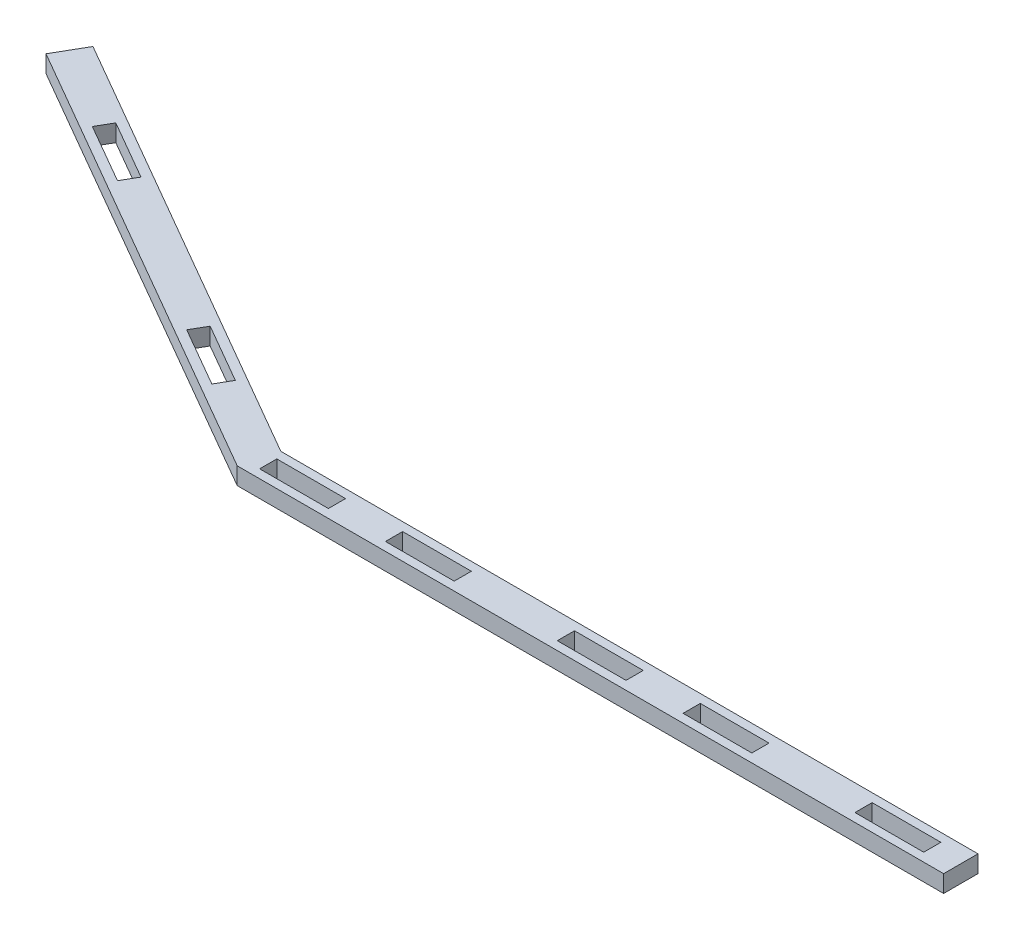
SolidWorks part; units mm, degrees
material "Cedar"
ref_plane "Front Plane" through (0, 0, 0) normal (0, 0, 1) x (1, 0, 0)
ref_plane "Top Plane" through (0, 0, 0) normal (0, 1, 0) x (1, 0, 0)
ref_plane "Right Plane" through (0, 0, 0) normal (1, 0, 0) x (0, 0, -1)
sketch "Sketch4" plane through (0, 0, 0) normal (0, 1, 0) x (1, 0, 0)
  line L0 (-428.2056, 90.1761) -> (-421.8556, 101.1746)
  line L1 (-421.8556, 101.1746) -> (-257.6145, 6.35)
  line L2 (-428.2056, 90.1761) -> (-261.0175, -6.35)
  line L3 (0, -6.35) -> (0, 6.35)
  line L4 (0, 6.35) -> (-257.6145, 6.35)
  line L5 (0, -6.35) -> (-261.0175, -6.35)
  line L6 (-396.3722, 75.4632) -> (-374.3751, 62.7632)
  line L7 (-374.3751, 62.7632) -> (-371.2001, 68.2625)
  line L8 (-371.2001, 68.2625) -> (-393.1972, 80.9625)
  line L9 (-393.1972, 80.9625) -> (-396.3722, 75.4632)
  line L10 (-313.8833, 27.8382) -> (-291.8862, 15.1382)
  line L11 (-291.8862, 15.1382) -> (-288.7112, 20.6375)
  line L12 (-288.7112, 20.6375) -> (-310.7083, 33.3375)
  line L13 (-310.7083, 33.3375) -> (-313.8833, 27.8382)
  line L14 (-255.9131, 3.175) -> (-255.9131, -3.175)
  line L15 (-255.9131, -3.175) -> (-230.5131, -3.175)
  line L16 (-230.5131, -3.175) -> (-230.5131, 3.175)
  line L17 (-230.5131, 3.175) -> (-255.9131, 3.175)
  line L18 (-209.4278, 3.175) -> (-209.4278, -3.175)
  line L19 (-209.4278, -3.175) -> (-184.0278, -3.175)
  line L20 (-184.0278, -3.175) -> (-184.0278, 3.175)
  line L21 (-184.0278, 3.175) -> (-209.4278, 3.175)
  line L22 (-120.5278, -3.175) -> (-120.5278, 3.175)
  line L23 (-120.5278, 3.175) -> (-145.9278, 3.175)
  line L24 (-145.9278, 3.175) -> (-145.9278, -3.175)
  line L25 (-145.9278, -3.175) -> (-120.5278, -3.175)
  line L26 (-99.4426, 3.175) -> (-99.4426, -3.175)
  line L27 (-99.4426, -3.175) -> (-74.0426, -3.175)
  line L28 (-74.0426, -3.175) -> (-74.0426, 3.175)
  line L29 (-74.0426, 3.175) -> (-99.4426, 3.175)
  line L30 (-10.5426, -3.175) -> (-10.5426, 3.175)
  line L31 (-10.5426, 3.175) -> (-35.9426, 3.175)
  line L32 (-35.9426, 3.175) -> (-35.9426, -3.175)
  line L33 (-35.9426, -3.175) -> (-10.5426, -3.175)
  point P34 (0, 0)
  dimension "D1" = 12.7
  dimension "D2" = 261.0175
  dimension "D5" = 193.0522
  dimension "D6" = 12.7
  dimension "D7" = 34.925
  dimension "D8" = 6.35
  dimension "D9" = 25.4
  dimension "D10" = 3.175
  dimension "D11" = 25.4
  dimension "D12" = 6.35
  dimension "D13" = 69.85
  dimension "D14" = 25.4
  dimension "D15" = 6.35
  dimension "D16" = 25.4
  dimension "D17" = 6.35
  dimension "D18" = 3.175
  dimension "D19" = 10.5426
  dimension "D20" = 25.4
  dimension "D21" = 6.35
  dimension "D22" = 25.4
  dimension "D23" = 6.35
  dimension "D24" = 3.175
  dimension "D25" = 38.1
  dimension "D26" = 6.35
  dimension "D27" = 25.4
  dimension "D28" = 6.35
  dimension "D29" = 25.4
  dimension "D30" = 3.175
  dimension "D31" = 21.0852
  dimension "D32" = 6.35
  dimension "D33" = 25.4
  dimension "D34" = 6.35
  dimension "D35" = 25.4
  dimension "D36" = 3.175
  dimension "D37" = 38.1
  dimension "D38" = 6.35
  dimension "D39" = 25.4
  dimension "D40" = 6.35
  dimension "D41" = 25.4
  dimension "D42" = 3.175
  dimension "D43" = 21.0852
  dimension "D44" = 6.35
  dimension "D45" = 25.4
  dimension "D46" = 6.35
  dimension "D47" = 25.4
  dimension "D48" = 3.175
  dimension "D49" = 257.6145
  dimension "D50" = 189.6493
extrude "Boss-Extrude2" add sketch "Sketch4" along normal blind 6.35
